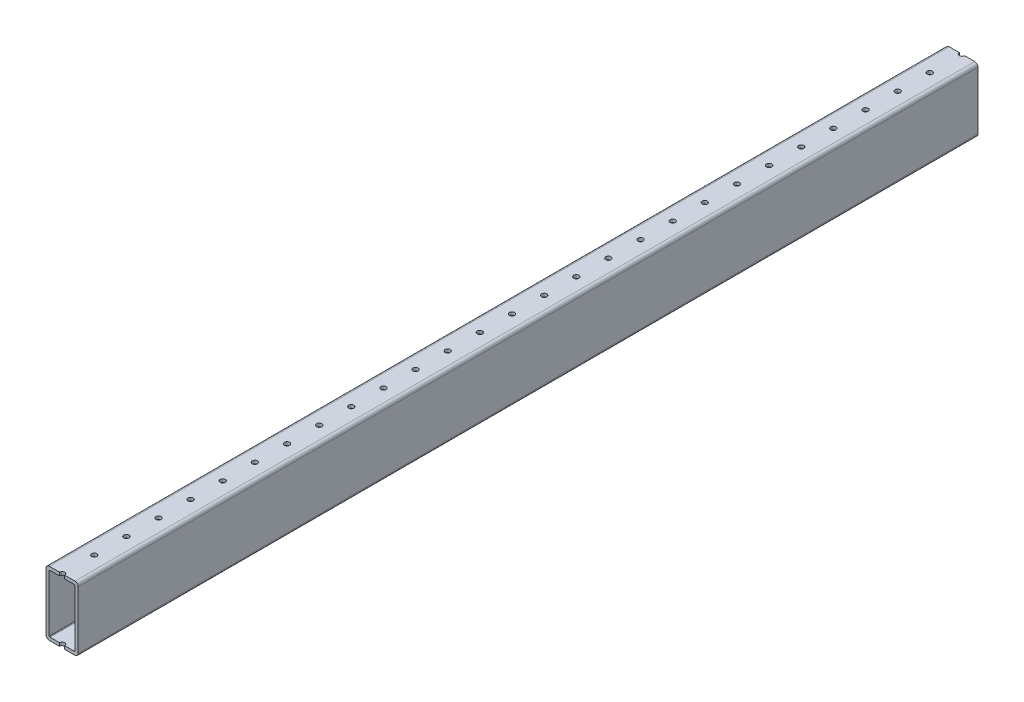
SolidWorks part; units mm, degrees
ref_plane "Front Plane" through (0, 0, 0) normal (0, 0, 1) x (1, 0, 0)
ref_plane "Top Plane" through (0, 0, 0) normal (0, 1, 0) x (1, 0, 0)
ref_plane "Right Plane" through (0, 0, 0) normal (1, 0, 0) x (0, 0, -1)
ref_plane "Plane1" through (12.7, 0, 0) normal (1, 0, 0) x (0, 0, -1)
sketch "Sketch1" plane through (12.7, 0, 0) normal (1, 0, 0) x (0, 0, -1)
  line L0 (355.6, -25.4) -> (355.6, 25.4)
  line L1 (355.6, 25.4) -> (-355.6, 25.4)
  line L2 (-355.6, 25.4) -> (-355.6, -25.4)
  line L3 (-355.6, -25.4) -> (355.6, -25.4)
  point P5 (0, 25.4)
  dimension "D1" = 50.8
  dimension "D2" = 25.4
  dimension "D3" = 711.2
extrude "Boss-Extrude1" add sketch "Sketch1" against normal blind 25.4
sketch "Sketch2" plane through (0, 0, -355.6) normal (0, 0, -1) x (-1, 0, 0)
  line L0 (10.16, -22.86) -> (10.16, 22.86)
  line L1 (10.16, 22.86) -> (-10.16, 22.86)
  line L2 (-10.16, 22.86) -> (-10.16, -22.86)
  line L3 (-10.16, -22.86) -> (10.16, -22.86)
extrude "Cut-Extrude1" cut sketch "Sketch2" against normal through all
hole_wizard "#6 Clearance Hole1" positions "Sketch4" profile "Sketch3" hole size "#6" standard "ANSI Inch"
sketch "Sketch4" plane through (0, -25.4, 0) normal (0, -1, 0) x (-1, 0, 0)
  point P0 (0, 711.2)
  point P1 (0, 736.6)
  point P2 (0, 685.8)
  point P3 (0, 660.4)
  point P4 (0, 635)
  point P5 (0, 609.6)
  point P6 (0, 584.2)
  point P7 (0, 558.8)
  point P8 (0, 533.4)
  point P9 (0, 508)
  point P10 (0, 482.6)
  point P11 (0, 457.2)
  point P12 (0, 431.8)
  point P13 (0, 406.4)
  point P14 (0, 381)
  point P15 (0, 355.6)
  point P16 (0, 330.2)
  point P17 (0, 304.8)
  point P18 (0, 279.4)
  point P19 (0, 254)
  point P20 (0, 228.6)
  point P21 (0, 203.2)
  point P22 (0, 177.8)
  point P23 (0, 152.4)
  point P24 (0, 127)
  point P25 (0, 101.6)
  point P26 (0, 76.2)
  point P27 (0, 50.8)
  point P28 (0, 25.4)
  point P29 (0, 0)
  point P30 (0, -25.4)
  point P31 (0, -50.8)
  point P32 (0, -76.2)
  point P33 (0, -101.6)
  point P34 (0, -127)
  point P35 (0, -152.4)
  point P36 (0, -177.8)
  point P37 (0, -203.2)
  point P38 (0, -228.6)
  point P39 (0, -254)
  point P40 (0, -279.4)
  point P41 (0, -304.8)
  point P42 (0, -330.2)
  point P43 (0, -355.6)
  point P44 (0, -381)
  point P45 (0, -406.4)
  point P46 (0, -431.8)
  point P47 (0, -457.2)
  point P48 (0, -482.6)
  point P49 (0, -508)
  point P50 (0, -533.4)
  point P51 (0, -558.8)
  point P52 (0, -584.2)
  point P53 (0, -609.6)
  point P54 (0, -635)
  point P55 (0, -660.4)
  point P56 (0, -685.8)
  point P57 (0, -711.2)
  point P58 (0, -736.6)
sketch "Sketch3" plane through (0, -25.4, -711.2) normal (1, 0, 0) x (0, 0, -1)
  line L0 (0, 0) -> (0, 50.8)
  line L1 (0, 50.8) -> (2.0701, 50.8)
  line L2 (2.0701, 50.8) -> (2.0701, 0)
  line L5 (2.0701, 0) -> (0, 0)
  line L11 (0, -6.35) -> (0, 107.95) construction
  dimension "Thru Hole Dia." = 4.1402
  dimension "Thru Hole Depth" = 50.8
hole_wizard "#6 Clearance Hole2" positions "Sketch6" profile "Sketch5" hole size "#6" standard "ANSI Inch"
sketch "Sketch6" plane through (0, 25.4, 0) normal (0, 1, 0) x (1, 0, 0)
  point P0 (0, 711.2)
  point P1 (0, 736.6)
  point P2 (0, 685.8)
  point P3 (0, 660.4)
  point P4 (0, 635)
  point P5 (0, 609.6)
  point P6 (0, 584.2)
  point P7 (0, 558.8)
  point P8 (0, 533.4)
  point P9 (0, 508)
  point P10 (0, 482.6)
  point P11 (0, 457.2)
  point P12 (0, 431.8)
  point P13 (0, 406.4)
  point P14 (0, 381)
  point P15 (0, 355.6)
  point P16 (0, 330.2)
  point P17 (0, 304.8)
  point P18 (0, 279.4)
  point P19 (0, 254)
  point P20 (0, 228.6)
  point P21 (0, 203.2)
  point P22 (0, 177.8)
  point P23 (0, 152.4)
  point P24 (0, 127)
  point P25 (0, 101.6)
  point P26 (0, 76.2)
  point P27 (0, 50.8)
  point P28 (0, 25.4)
  point P29 (0, 0)
  point P30 (0, -25.4)
  point P31 (0, -50.8)
  point P32 (0, -76.2)
  point P33 (0, -101.6)
  point P34 (0, -127)
  point P35 (0, -152.4)
  point P36 (0, -177.8)
  point P37 (0, -203.2)
  point P38 (0, -228.6)
  point P39 (0, -254)
  point P40 (0, -279.4)
  point P41 (0, -304.8)
  point P42 (0, -330.2)
  point P43 (0, -355.6)
  point P44 (0, -381)
  point P45 (0, -406.4)
  point P46 (0, -431.8)
  point P47 (0, -457.2)
  point P48 (0, -482.6)
  point P49 (0, -508)
  point P50 (0, -533.4)
  point P51 (0, -558.8)
  point P52 (0, -584.2)
  point P53 (0, -609.6)
  point P54 (0, -635)
  point P55 (0, -660.4)
  point P56 (0, -685.8)
  point P57 (0, -711.2)
  point P58 (0, -736.6)
sketch "Sketch5" plane through (0, 25.4, -711.2) normal (1, 0, 0) x (0, 0, 1)
  line L0 (0, 0) -> (0, 50.8)
  line L1 (0, 50.8) -> (2.0701, 50.8)
  line L2 (2.0701, 50.8) -> (2.0701, 0)
  line L5 (2.0701, 0) -> (0, 0)
  line L11 (0, -6.35) -> (0, 107.95) construction
  dimension "Thru Hole Dia." = 4.1402
  dimension "Thru Hole Depth" = 50.8
fillet "Fillet1" radius 0.5 4 edges at (10.16, 22.86, 0) (-10.16, -22.86, 0) (-10.16, 22.86, 0) (10.16, -22.86, 0)
fillet "Fillet2" radius 2.54 4 edges at (12.7, 25.4, 0) (-12.7, -25.4, 0) (12.7, -25.4, 0) (-12.7, 25.4, 0)
